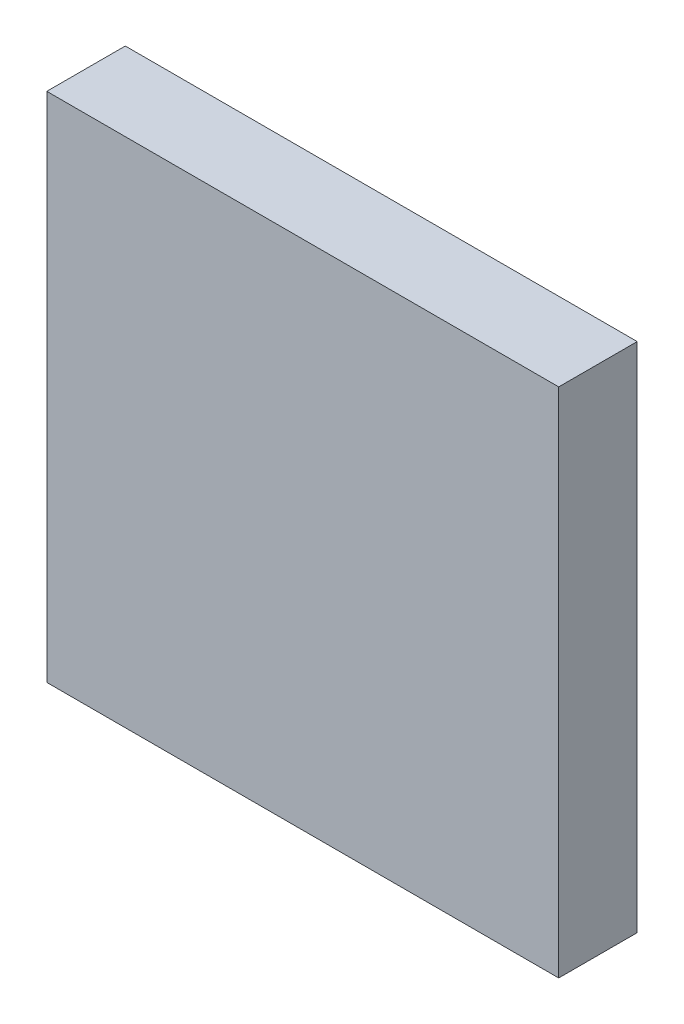
SolidWorks part; units mm, degrees
ref_plane "前视基准面" through (0, 0, 0) normal (0, 0, 1) x (1, 0, 0)
ref_plane "上视基准面" through (0, 0, 0) normal (0, 1, 0) x (1, 0, 0)
ref_plane "右视基准面" through (0, 0, 0) normal (1, 0, 0) x (0, 0, -1)
sketch "草图1" plane through (0, 0, 0) normal (0, 0, 1) x (1, 0, 0)
  line L0 (46.8075, 23.2816) -> (61.8075, 23.2816)
  line L1 (46.8075, 38.2816) -> (61.8075, 38.2816)
  line L2 (46.8075, 38.2816) -> (46.8075, 23.2816)
  line L3 (61.8075, 38.2816) -> (61.8075, 23.2816)
  dimension "D1" = 15
  dimension "D2" = 15
extrude "凸台-拉伸1" add sketch "草图1" along normal blind 2.3
